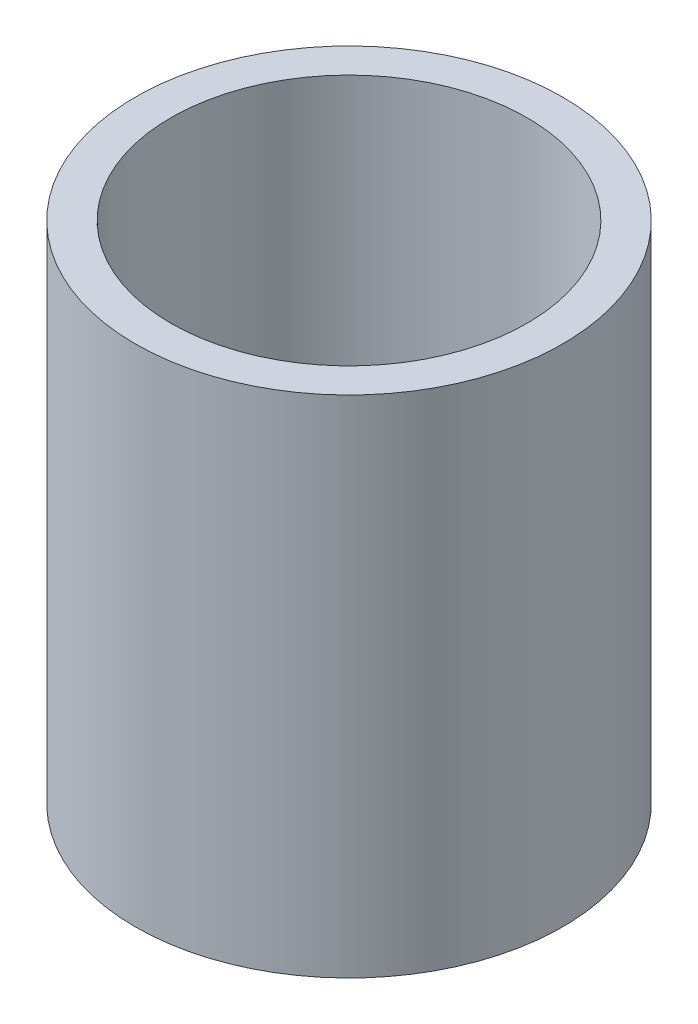
SolidWorks part; units mm, degrees
ref_plane "Front Plane" through (0, 0, 0) normal (0, 0, 1) x (1, 0, 0)
ref_plane "Top Plane" through (0, 0, 0) normal (0, 1, 0) x (1, 0, 0)
ref_plane "Right Plane" through (0, 0, 0) normal (1, 0, 0) x (0, 0, -1)
sketch "Sketch1" plane through (0, 0, 0) normal (0, 1, 0) x (1, 0, 0)
  circle A0 centre (0, 0) radius 38.1
  dimension "D1" = 76.2
extrude "Boss-Extrude1" add sketch "Sketch1" along normal blind 90
ref_plane "Plane1" through (0, 90, 0) normal (0, 1, 0) x (1, 0, 0)
sketch "Sketch5" plane through (0, 90, 0) normal (0, 1, 0) x (1, 0, 0)
  circle A0 centre (0, 0) radius 31.75
  dimension "D1" = 63.5
extrude "Cut-Extrude1" cut sketch "Sketch5" against normal blind 77.3
